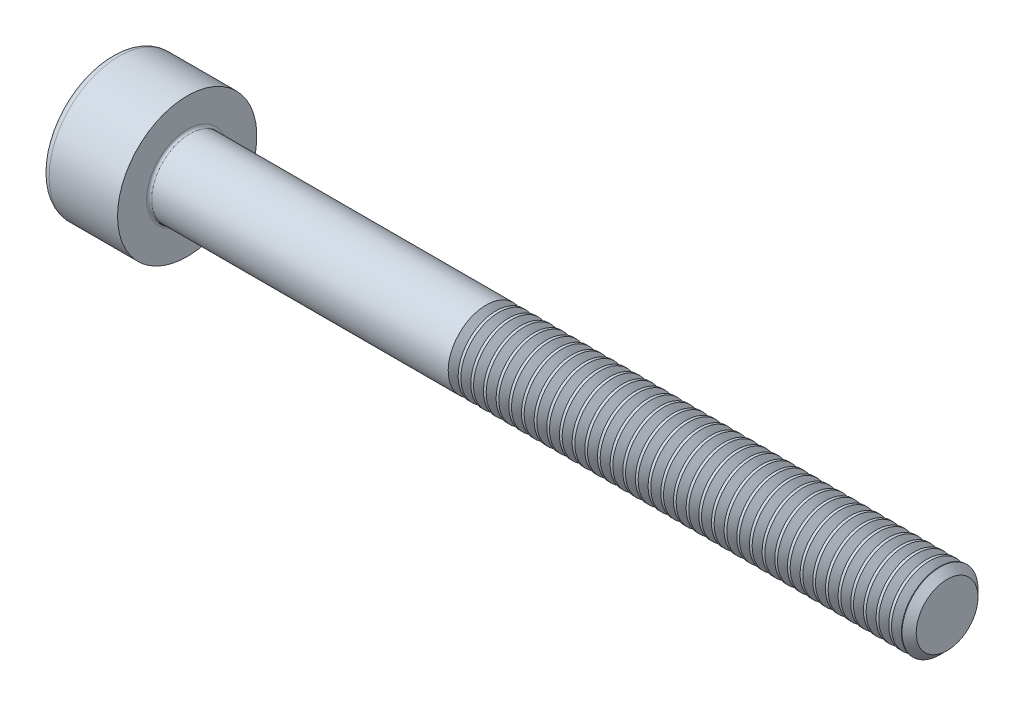
SolidWorks part; units mm, degrees
ref_plane "Plane1" through (0, 0, 0) normal (0, 0, 1) x (1, 0, 0)
ref_plane "Plane2" through (0, 0, 0) normal (0, 1, 0) x (1, 0, 0)
ref_plane "Plane3" through (0, 0, 0) normal (1, 0, 0) x (0, 0, -1)
sketch "BodySke" plane through (0, 0, 0) normal (0, 0, 1) x (1, 0, 0)
  line L0 (0, 0) -> (0, 2.75)
  line L1 (0, 2.75) -> (3, 2.75)
  line L2 (3, 2.75) -> (3, 1.5)
  line L3 (3, 1.5) -> (32.7195, 1.5)
  line L4 (33, 1.2195) -> (33, 0)
  line L5 (33, 0) -> (0, 0)
  line L6 (-31.75, 0) -> (127, 0) construction
  line L8 (33, 1.2195) -> (32.7195, 1.5)
  line L10 (33, -1.2195) -> (32.7195, -1.5) construction
  line L11 (3.5, 9.525) -> (3.5, 3.175) construction
  line L12 (15, 9.525) -> (15, 3.175) construction
  line L13 (-27, 9.525) -> (-27, 3.175) construction
  dimension "Diameter" = 3
  dimension "Head_ht" = 3
  dimension "Length" = 30
  dimension "Body_ch_ang" = 45
  dimension "Head_dia" = 5.5
  dimension "Minor_dia" = 2.439
  dimension "Advance" = 0.5
  dimension "Thread_nom" = 18
  dimension "Thread_length" = 60
revolve "Base-Revolve" add sketch "BodySke"
cosmetic thread "ThreadCosmetic" [suppressed]
fillet "Fillet1" radius 0.1 1 edges at (3, 0, 1.5)
fillet "Fillet2" radius 0.3 1 edges at (0, 0, 2.75)
sketch "Sketch2" plane through (0, 0, 0) normal (0, 0, 1) x (1, 0, 0)
  line L0 (0, 1.26) -> (1.3, 1.26)
  line L1 (1.3, 1.26) -> (2.0275, 0)
  line L2 (-31.75, 0) -> (127, 0) construction
  line L3 (2.0275, 0) -> (0, 0)
  line L4 (0, 0) -> (0, 1.26)
  line L6 (0, 0) -> (47.625, 0) construction
  dimension "D1" = 1.26
  dimension "D2" = 60
  dimension "Depth" = 1.3
revolve "Hex-PreBroach" cut sketch "Sketch2" angle 360 about L6
sketch "Sketch3" plane through (0, 0, 0) normal (-1, 0, 0) x (0, 0.5, 0.866)
  line L0 (0.7275, 1.26) -> (-0.7275, 1.26)
  line L1 (-0.7275, 1.26) -> (-1.4549, 0)
  line L2 (0.7275, 1.26) -> (1.4549, 0)
  line L3 (0.7275, -1.26) -> (1.4549, 0)
  line L4 (0.7275, -1.26) -> (-0.7275, -1.26)
  line L5 (-0.7275, -1.26) -> (-1.4549, 0)
  dimension "D1" = 1.26
  dimension "D2" = 1.26
  dimension "Hex_size" = 2.52
extrude "Hex" cut sketch "Sketch3" against normal blind 1.3
sketch "ThdSchSke" plane through (0, 0, 0) normal (0, 0, 1) x (1, 0, 0)
  line L0 (15, -1.2195) -> (14.8036, -1.5)
  line L1 (15, -1.2195) -> (15.1964, -1.5)
  line L2 (15.1964, -1.5) -> (15.1964, -1.875)
  line L3 (-3.175, 0) -> (5.1513, 0) construction
  line L4 (0, 2.45) -> (0, -2.45) construction
  line L5 (15.1964, -1.875) -> (14.8036, -1.875)
  line L6 (14.8036, -1.875) -> (14.8036, -1.5)
  dimension "Thread_minor" = 2.439
  dimension "Diameter" = 3
  dimension "Start" = 15
  dimension "SideAngle" = 55
  dimension "VeeAngle" = 70
  dimension "Overcut" = 3.75
revolve "ThreadSchematic" cut sketch "ThdSchSke" angle 360 about L3
pattern_linear "ThdSchPat" count 36 spacing 0.5 along (1, 0, 0) of "ThreadSchematic"
equation "\"D2@Sketch3\" = \"Hex_size@Sketch3\" / 2"
equation "\"D1@Sketch3\" = \"Hex_size@Sketch3\" / 2"
equation "\"D1@Sketch2\" = \"Hex_size@Sketch3\" / 2"
equation "\"Thread_minor@ThreadCosmetic\"  =  \"Minor_dia@BodySke\""
equation "\"Depth@Sketch2\" =  \"Key_eng@Hex\""
equation "\"Thread_length@ThreadCosmetic\" = ((sgn( (\"Length@BodySke\" - \"Advance@BodySke\" * 3.0) - \"Thread_nom@BodySke\" )-1)*( (\"Length@BodySke\" - \"Advance@BodySke\" * 3.0) - \"Thread_nom@BodySke\" ))/-2+ \"Thread_nom@BodySke\""
equation "\"Thread_minor@ThdSchSke\" = \"Minor_dia@BodySke\""
equation "\"Diameter@ThdSchSke\" = \"Diameter@BodySke\""
equation "\"Overcut@ThdSchSke\" = \"Diameter@BodySke\" * 1.25"
equation "\"Start@ThdSchSke\" = \"Head_ht@BodySke\" + \"Length@BodySke\" - \"Thread_length@ThreadCosmetic\"  '---Non-countersunk---"
equation "\"Num_threads@ThdSchPat\" = int( \"Thread_length@ThreadCosmetic\" / \"Advance@BodySke\" + 0.999 )  + 1"
equation "\"Advance@ThdSchPat\" = \"Thread_length@ThreadCosmetic\" /  (\"Num_threads@ThdSchPat\" - 1) 'relax it"
equation "\"Num_threads@ThdSchPat\" = \"Num_threads@ThdSchPat\" - sgn( \"Num_threads@ThdSchPat\" - 1) '---chamfered tips only---"
